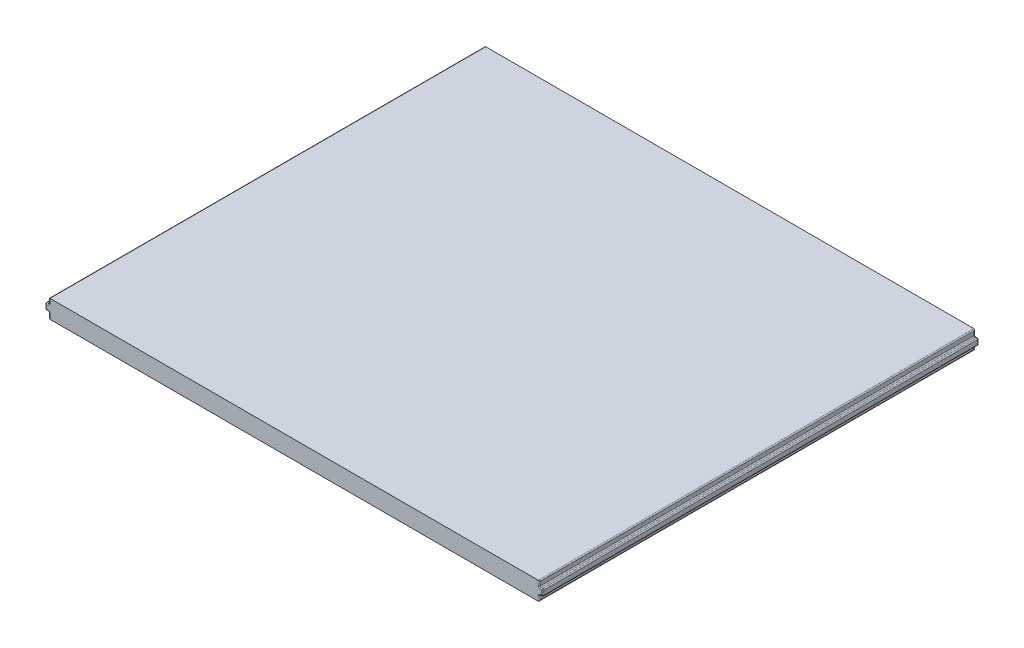
SolidWorks part; units mm, degrees
ref_plane "Front Plane" through (0, 0, 0) normal (0, 0, 1) x (1, 0, 0)
ref_plane "Top Plane" through (0, 0, 0) normal (0, 1, 0) x (1, 0, 0)
ref_plane "Right Plane" through (0, 0, 0) normal (1, 0, 0) x (0, 0, -1)
sketch "Sketch1" plane through (0, 0, 0) normal (0, 1, 0) x (1, 0, 0)
  line L1 (1433.9721, 1066.4463) -> (1568.9721, 1066.4463)
  line L2 (1433.9721, 1066.4463) -> (1433.9721, 946.4463)
  line L3 (1433.9721, 946.4463) -> (1568.9721, 946.4463)
  line L4 (1568.9721, 1066.4463) -> (1568.9721, 946.4463)
  dimension "D1" = 135
  dimension "D2" = 120
extrude "Boss-Extrude1" add sketch "Sketch1" along normal blind 5
sketch "Sketch2" plane through (1568.9721, 0, 0) normal (1, 0, 0) x (0, 0, -1)
  line L1 (946.4463, 5) -> (946.4463, 0) construction
  line L2 (946.4463, 3.4) -> (1066.4463, 3.4)
  line L3 (946.4463, 3.4) -> (946.4463, 1.65)
  line L4 (946.4463, 1.65) -> (1066.4463, 1.65)
  line L5 (1066.4463, 3.4) -> (1066.4463, 1.65)
  line L6 (1066.4463, 5) -> (1066.4463, 0) construction
  line L7 (946.4463, 0) -> (1066.4463, 0) construction
  dimension "D1" = 1.75
  dimension "D2" = 1.65
extrude "Boss-Extrude2" add sketch "Sketch2" along normal blind 1
ref_plane "Plane1" through (1501.4721, 0, 0) normal (-1, 0, 0) x (0, 0, 1)
mirror "Mirror1" about plane through (1501.4721, 0, 0) normal (-1, 0, 0) of "Boss-Extrude2"
fillet "Fillet1" radius 0.3 32 edges at (1569.4721, 1.65, -1066.4463) (1569.4721, 1.65, -946.4463) (1569.4721, 3.4, -946.4463) (1569.4721, 3.4, -1066.4463) (1568.9721, 0.825, -1066.4463) (1568.9721, 0, -1006.4463) (1568.9721, 0.825, -946.4463) (1568.9721, 1.65, -1006.4463) (1569.9721, 3.4, -1006.4463) (1569.9721, 2.525, -1066.4463) (1569.9721, 1.65, -1006.4463) (1569.9721, 2.525, -946.4463) (1568.9721, 4.2, -946.4463) (1568.9721, 5, -1006.4463) (1568.9721, 4.2, -1066.4463) (1568.9721, 3.4, -1006.4463) (1433.4721, 1.65, -946.4463) (1433.4721, 1.65, -1066.4463) (1433.4721, 3.4, -1066.4463) (1433.4721, 3.4, -946.4463) (1433.9721, 0, -1006.4463) (1433.9721, 0.825, -1066.4463) (1433.9721, 1.65, -1006.4463) (1433.9721, 0.825, -946.4463) (1433.9721, 5, -1006.4463) (1433.9721, 4.2, -946.4463) (1433.9721, 3.4, -1006.4463) (1433.9721, 4.2, -1066.4463) (1432.9721, 1.65, -1006.4463) (1432.9721, 2.525, -946.4463) (1432.9721, 2.525, -1066.4463) (1432.9721, 3.4, -1006.4463)
